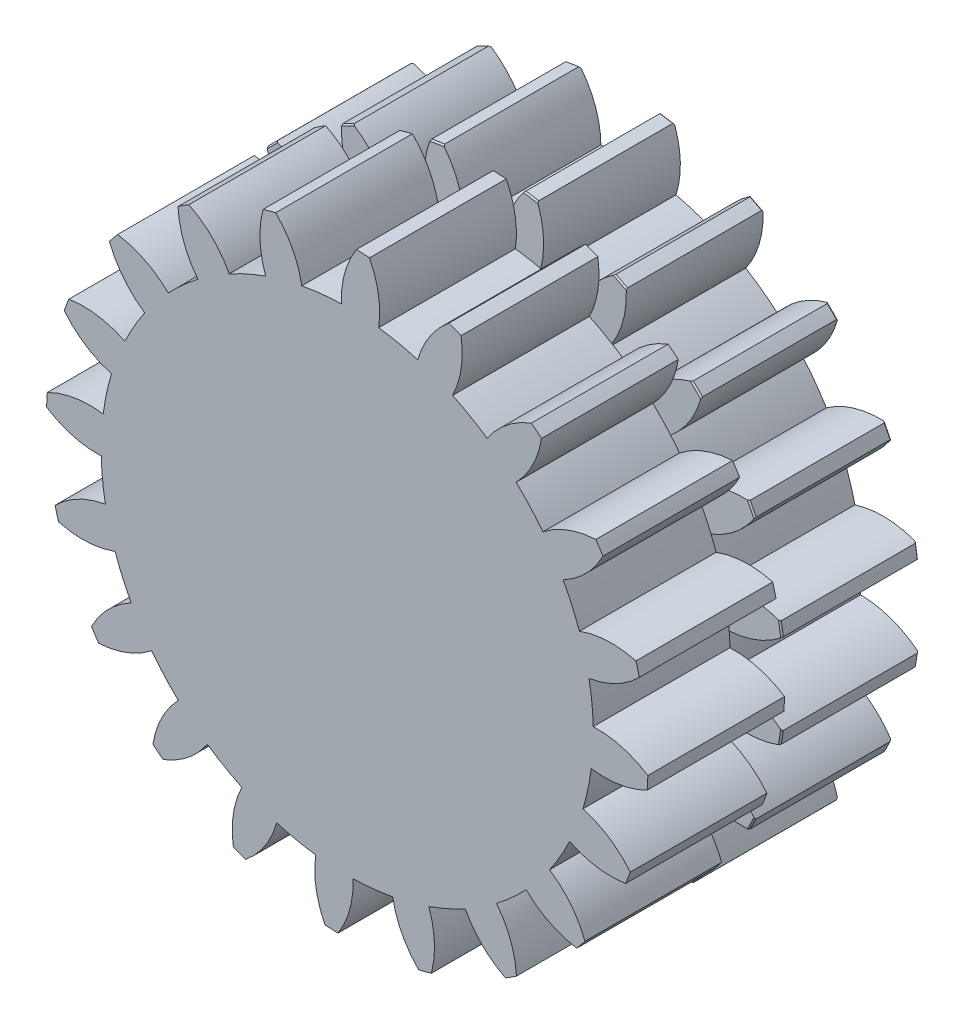
SolidWorks part; units mm, degrees
ref_plane "Front Plane" through (0, 0, 0) normal (0, 0, 1) x (1, 0, 0)
ref_plane "Top Plane" through (0, 0, 0) normal (0, 1, 0) x (1, 0, 0)
ref_plane "Right Plane" through (0, 0, 0) normal (1, 0, 0) x (0, 0, -1)
sketch "Sketch2" plane through (0, 0, 0) normal (0, 0, 1) x (1, 0, 0)
  circle A0 centre (0, 0) radius 20 construction
  circle A1 centre (0, 0) radius 22
  dimension "pitch cirlcle" = 40
  dimension "pitch circle 2" = 44
extrude "Boss-Extrude1" add sketch "Sketch2" along normal mid plane 10
sketch "Sketch3" plane through (0, 0, 5) normal (0, 0, 1) x (1, 0, 0)
  line L0 (0, 0) -> (0, 22) construction
  line L1 (6.7984, 20.9232) -> (0, 0) construction
  line L2 (0, 0) -> (3.4416, 21.7291) construction
  line L3 (0, 0) -> (-1.1551, 17.9629) construction
  line L4 (-1.5692, 19.9383) -> (1.5692, 19.9383) construction
  line L5 (1.5692, 19.9383) -> (4.6689, 19.4474) construction
  line L6 (0, 15.6271) -> (-2.2766, 21.8819) construction
  arc A0 (1.1551, 17.9629) -> (-1.1551, 17.9629) centre (0, 0) ccw
  circle A2 centre (0, 0) radius 22 construction
  circle A3 centre (0, 0) radius 19.75 construction
  arc A4 (-2.6166, 21.8438) -> (-1.1551, 17.9629) centre (-8.2502, 17.5067) cw
  arc A5 (2.6166, 21.8438) -> (1.1551, 17.9629) centre (8.2502, 17.5067) ccw
  circle A6 centre (0, 0) radius 20 construction
  circle A7 centre (0, 0) radius 22 construction
  arc A8 (2.6166, 21.8438) -> (-2.6166, 21.8438) centre (0, 0) ccw
  dimension "angle displacement" = 18
  dimension "dedenum" = 4
  dimension "addendum" = 2.25
  dimension "Pressure Angle" = 20
extrude "Cut-Extrude1" cut sketch "Sketch3" against normal blind 10
fillet "Fillet1" radius 0.6 2 edges at (1.1551, 17.9629, 0) (-1.1551, 17.9629, 0)
chamfer "Chamfer1" distance 0.1 2 edges at (0, -22, -5) (0, -22, 5)
pattern_circular "CirPattern1" count 20 over 360 about axis through (0, 0, 0) along (0, 0, 1) of "Cut-Extrude1", "Fillet1"
sketch "Sketch6" plane through (0, 0, 5) normal (0, 0, 1) x (1, 0, 0)
  line L0 (-2.969, 21.7987) -> (-2.3981, 24.057)
  line L1 (-2.3981, 24.057) -> (2.7785, 23.6602)
  line L2 (2.7785, 23.6602) -> (2.969, 21.7987)
  arc A0 (-1.445, 17.5517) -> (-2.969, 21.7987) centre (-8.2502, 17.5067) ccw
  arc A1 (2.969, 21.7987) -> (1.445, 17.5517) centre (8.2502, 17.5067) ccw
  arc A2 (-2.5466, 21.7514) -> (-2.6166, 21.8438) centre (-8.2502, 17.5067) ccw construction
  arc A3 (2.6166, 21.8438) -> (2.5466, 21.7514) centre (8.2502, 17.5067) ccw construction
  arc A4 (-2.6166, 21.8438) -> (-4.2616, 21.5833) centre (0, 0) ccw construction
  arc A5 (4.2616, 21.5833) -> (2.6166, 21.8438) centre (0, 0) ccw construction
  arc A7 (1.445, 17.5517) -> (-1.445, 17.5517) centre (0, 0) ccw
extrude "Cut-Extrude3" cut sketch "Sketch6" against normal through all
pattern_circular "CirPattern2" count 20 over 360 about axis through (0, 0, 0) along (0, 0, 1) of "Cut-Extrude3"
ref_point "Point1"
sketch "Sketch8" plane through (0, 0, 5) normal (0, 0, 1) x (1, 0, 0)
  circle A1 centre (0, 0) radius 22
extrude "Boss-Extrude2" add sketch "Sketch8" along normal blind 10
sketch "Sketch9" plane through (0, 0, 15) normal (0, 0, 1) x (1, 0, 0)
  line L0 (-8.2502, 17.5067) -> (0, 0) construction
  line L1 (0, 0) -> (-4.43, 18.8394) construction
  line L2 (11.7097, 15.4088) -> (0, 0) construction
  line L3 (8.2502, 17.5067) -> (0, 0) construction
  arc A0 (2.6049, 17.8105) -> (1.9822, 21.9105) centre (-4.43, 18.8394) ccw
  arc A1 (7.101, 20.8225) -> (4.8645, 17.3302) centre (11.7097, 15.4088) ccw
  arc A2 (-1.1551, 17.9629) -> (-2.6166, 21.8438) centre (-8.2502, 17.5067) ccw construction
  arc A3 (2.6166, 21.8438) -> (1.1551, 17.9629) centre (8.2502, 17.5067) ccw construction
  circle A5 centre (0, 0) radius 19.3533 construction
  arc A6 (4.8645, 17.3302) -> (2.6049, 17.8105) centre (0, 0) ccw
  arc A7 (21.0387, 6.4322) -> (1.9822, 21.9105) centre (0, 0) ccw
  arc A8 (2.6166, 21.8438) -> (-2.6166, 21.8438) centre (0, 0) ccw construction
  arc A10 (21.0387, 6.4322) -> (1.9822, 21.9105) centre (0, 0) ccw
  arc A11 (21.0387, 6.4322) -> (1.9822, 21.9105) centre (0, 0) ccw
  circle M9 centre (0, 0) radius 22
  dimension "D1" = 12
  dimension "D2" = 12
extrude "Cut-Extrude4" cut sketch "Sketch9" against normal blind 10 contours A6 A1 A0 M9
pattern_circular "CirPattern3" count 20 over 360 about axis through (0, 0, 0) along (0, 0, 1) of "Cut-Extrude4"
sketch "Sketch10" plane through (0, 0, 15) normal (0, 0, 1) x (1, 0, 0)
  line L3 (-5.2313, 21.369) -> (-4.1683, 24.0217)
  line L4 (-4.1683, 24.0217) -> (0.5688, 23.6427)
  line L5 (0.5688, 23.6427) -> (0.6741, 21.9897)
  arc A3 (-3.326, 17.69) -> (-5.2313, 21.369) centre (-10.0349, 16.5484) ccw
  arc A4 (0.6741, 21.9897) -> (-0.4246, 17.995) centre (6.375, 18.2731) ccw
  arc A5 (-0.4246, 17.995) -> (-3.326, 17.69) centre (0, 0) ccw
  arc A8 (-3.0264, 17.7438) -> (-4.8855, 21.4507) centre (-10.0349, 16.5484) ccw construction
  arc A9 (0.3189, 21.9977) -> (-0.7289, 17.9852) centre (6.375, 18.2731) ccw construction
  arc A10 (-4.8855, 21.4507) -> (-6.4943, 21.0196) centre (0, 0) ccw construction
  arc A11 (1.9822, 21.9105) -> (0.3189, 21.9977) centre (0, 0) ccw construction
  dimension "D1" = 13.6107
extrude "Cut-Extrude5" cut sketch "Sketch10" against normal blind 10
pattern_circular "CirPattern4" count 20 over 360 about axis through (0, 0, 0) along (0, 0, 1) of "Cut-Extrude5"
equation "\"module\"= 2mm"
equation "\"number of teeth\"= 20"
equation "\"pressure angle\"= 20"
equation "\"pitch cirlcle@Sketch2\"= \"module\" * \"number of teeth\""
equation "\"pitch circle 2@Sketch2\"= \"module\" * ( \"number of teeth\" + 2 )"
equation "\"angle displacement@Sketch3\"= 360 / \"number of teeth\""
equation "\"addendum@Sketch3\"= IIF ( \"module\" >= 1.25 , 2.25 , 2.4 )"
equation "\"Pressure Angle@Sketch3\"= \"pressure angle\""
equation "\"D1@CirPattern1\"= \"number of teeth\""
equation "\"D1@Fillet1\"= 0.3 * \"module\""
equation "\"D1@CirPattern2\"=\"number of teeth\""
equation "\"D1@CirPattern3\"=\"number of teeth\""
